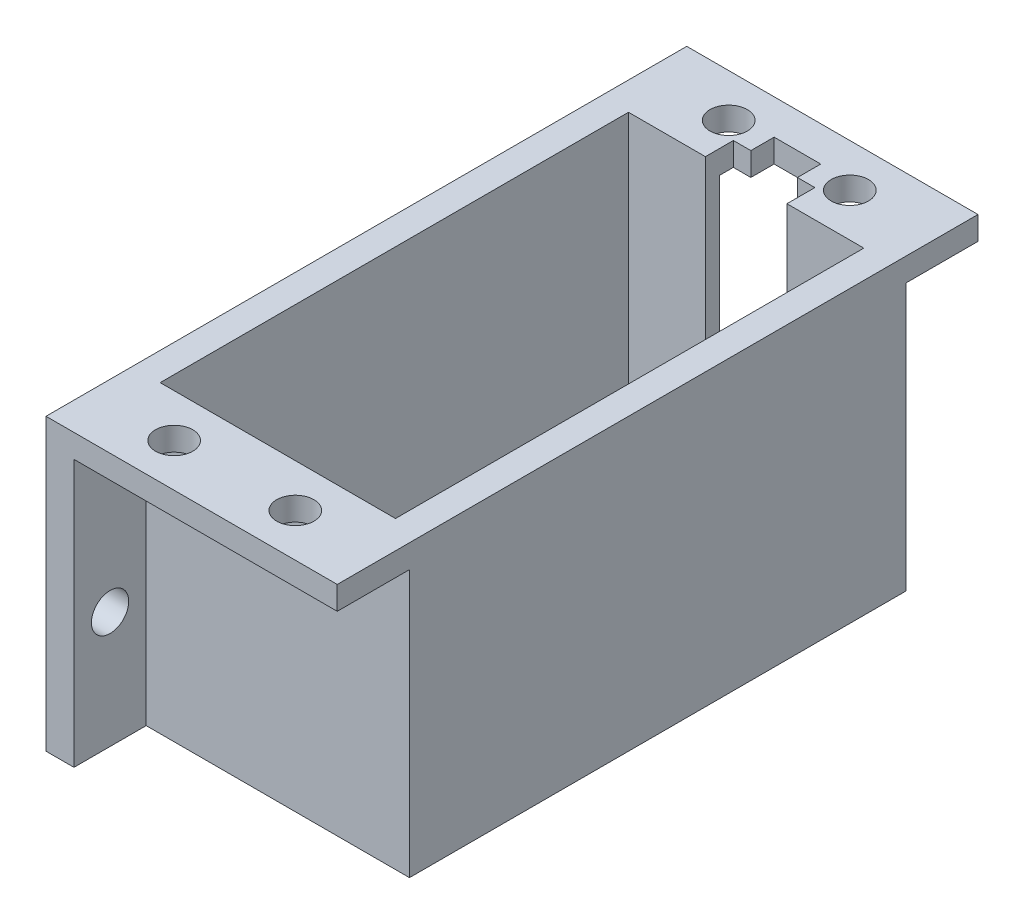
SolidWorks part; units mm, degrees
ref_plane "Front Plane" through (0, 0, 0) normal (0, 0, 1) x (1, 0, 0)
ref_plane "Top Plane" through (0, 0, 0) normal (0, 1, 0) x (1, 0, 0)
ref_plane "Right Plane" through (0, 0, 0) normal (1, 0, 0) x (0, 0, -1)
sketch "Sketch2" plane through (0, 0, 0) normal (0, 1, 0) x (1, 0, 0)
  line L1 (-37.5, 4) -> (37.5, 4)
  line L2 (-37.5, 4) -> (-37.5, -4)
  line L3 (-37.5, -4) -> (37.5, -4)
  line L4 (37.5, 4) -> (37.5, -4)
  line L5 (-37.5, 4) -> (37.5, -4) construction
  line L6 (-37.5, -4) -> (37.5, 4) construction
  circle A1 centre (-31.75, 0) radius 1.6
  circle A2 centre (31.75, 0) radius 1.6
  point P0 (0, 0)
extrude "Boss-Extrude1" add sketch "Sketch2" along normal blind 2
sketch "Sketch3" plane through (0, 2, 0) normal (0, 1, 0) x (1, 0, 0)
  line L1 (-12.5, -22.5) -> (12.5, -22.5)
  line L2 (-12.5, -22.5) -> (-12.5, -4)
  line L3 (-37.5, -4) -> (37.5, -4) construction
  line L4 (-12.5, -4) -> (12.5, -4)
  line L5 (12.5, -4) -> (12.5, -22.5)
  point P0 (0, -4)
  point P6 (0, -22.5)
extrude "Boss-Extrude2" add sketch "Sketch3" against normal up to surface (2 mm away) up to face at (0, 0, 0)
sketch "Sketch4" plane through (0, 0, -4) normal (0, 0, -1) x (-1, 0, 0)
  line L4 (-12.5, 0) -> (12.5, 0)
  line L5 (-12.5, 2) -> (-12.5, 0)
  line L6 (12.5, 2) -> (-12.5, 2)
  line L7 (12.5, 0) -> (12.5, 2)
  line L8 (-12.5, 0) -> (12.5, 0)
  line L9 (-12.5, 2) -> (-12.5, 0)
  line L10 (12.5, 2) -> (-12.5, 2)
  line L11 (12.5, 0) -> (12.5, 2)
  dimension "D1" = 0
extrude "Boss-Extrude3" add sketch "Sketch4" along normal blind 18.5
sketch "Sketch5" plane through (0, 2, 0) normal (0, 1, 0) x (1, 0, 0)
  line L1 (-5.1, 20.1) -> (5.1, 20.1)
  line L2 (-5.1, 20.1) -> (-5.1, -20.1)
  line L3 (-5.1, -20.1) -> (5.1, -20.1)
  line L4 (5.1, 20.1) -> (5.1, -20.1)
  line L5 (-5.1, 20.1) -> (5.1, -20.1) construction
  line L6 (-5.1, -20.1) -> (5.1, 20.1) construction
  point P0 (0, 0)
extrude "Cut-Extrude1" cut sketch "Sketch5" against normal blind 18.5
sketch "Sketch6" plane through (0, 2, 0) normal (0, 1, 0) x (1, 0, 0)
  line L0 (-12.5, 4) -> (-12.5, -4)
  line L1 (12.5, 4) -> (12.5, -4)
  line L3 (-5.1, 20.1) -> (5.1, 20.1)
  line L4 (-5.1, 20.1) -> (-5.1, -20.1)
  line L5 (-5.1, -20.1) -> (5.1, -20.1)
  line L6 (5.1, 20.1) -> (5.1, -20.1)
  line L12 (37.5, -4) -> (37.5, 4)
  line L13 (37.5, 4) -> (12.5, 4)
  line L14 (12.5, 4) -> (12.5, 22.5)
  line L15 (12.5, 22.5) -> (-12.5, 22.5)
  line L16 (-12.5, 22.5) -> (-12.5, 4)
  line L17 (-12.5, 4) -> (-37.5, 4)
  line L18 (-37.5, 4) -> (-37.5, -4)
  line L19 (-37.5, -4) -> (-12.5, -4)
  line L20 (-12.5, -4) -> (-12.5, -22.5)
  line L21 (-12.5, -22.5) -> (12.5, -22.5)
  line L22 (12.5, -22.5) -> (12.5, -4)
  line L23 (12.5, -4) -> (37.5, -4)
  line L26 (12.5, 4) -> (12.5, 22.5)
  line L27 (12.5, 22.5) -> (-12.5, 22.5)
  line L28 (-12.5, 22.5) -> (-12.5, 4)
  line L32 (-12.5, -4) -> (-12.5, -22.5)
  line L33 (-12.5, -22.5) -> (12.5, -22.5)
  line L34 (12.5, -22.5) -> (12.5, -4)
  dimension "D1" = 0
extrude "Boss-Extrude4" add sketch "Sketch6" along normal blind 24.9
sketch "Sketch8" plane through (0, 26.9, 0) normal (0, 1, 0) x (1, 0, 0)
  line L1 (-12.5, 22.5) -> (12.5, 22.5)
  line L2 (-12.5, 22.5) -> (-12.5, 29.5)
  line L3 (-12.5, 29.5) -> (12.5, 29.5)
  line L4 (12.5, 22.5) -> (12.5, 29.5)
  line L5 (-12.5, -22.5) -> (12.5, -22.5)
  line L6 (-12.5, -22.5) -> (-12.5, -29.5)
  line L7 (-12.5, -29.5) -> (12.5, -29.5)
  line L8 (12.5, -22.5) -> (12.5, -29.5)
extrude "Boss-Extrude5" add sketch "Sketch8" against normal blind 2
sketch "Sketch9" plane through (0, 24.9, 0) normal (0, -1, 0) x (1, 0, 0)
  circle A1 centre (5.2, 23.8) radius 1.6
  circle A2 centre (-5.2, 23.8) radius 1.6
  circle A3 centre (-5.2, -23.8) radius 1.6
  circle A4 centre (5.2, -23.8) radius 1.6
extrude "Cut-Extrude2" cut sketch "Sketch9" against normal blind 2
sketch "Sketch10" plane through (0, 0, 0) normal (0, -1, 0) x (1, 0, 0)
  line L1 (-10.1, 20.1) -> (10.1, 20.1)
  line L2 (-10.1, 20.1) -> (-10.1, -20.1)
  line L3 (-10.1, -20.1) -> (10.1, -20.1)
  line L4 (10.1, 20.1) -> (10.1, -20.1)
  line L5 (-10.1, 20.1) -> (10.1, -20.1) construction
  line L6 (-10.1, -20.1) -> (10.1, 20.1) construction
  point P0 (0, 0)
extrude "Cut-Extrude3" cut sketch "Sketch10" against normal blind 77
sketch "Sketch11" plane through (0, 0, 0) normal (0, -1, 0) x (1, 0, 0)
  line L1 (3.5, -20.1) -> (3.5, -22.5)
  line L2 (12.5, -22.5) -> (-12.5, -22.5) construction
  line L3 (3.5, -22.5) -> (-3.5, -22.5)
  line L4 (-3.5, -22.5) -> (-3.5, -20.1)
  line L5 (-3.5, -20.1) -> (3.5, -20.1)
extrude "Cut-Extrude4" cut sketch "Sketch11" against normal blind 77
sketch "Sketch12" plane through (0, 0, 0) normal (0, -1, 0) x (1, 0, 0)
  line L0 (-12.5, 22.5) -> (-12.5, 29.5)
  line L1 (-12.5, 29.5) -> (-10.1, 29.5)
  line L2 (-12.5, 29.5) -> (12.5, 29.5) construction
  line L3 (-10.1, 29.5) -> (-10.1, 22.5)
  line L4 (12.5, 22.5) -> (6.1327, 22.5) construction
  line L5 (-10.1, 22.5) -> (-12.5, 22.5)
  line L6 (-12.5, -22.5) -> (-6.1327, -22.5) construction
  line L7 (-10.1, -22.5) -> (-12.5, -22.5)
  line L8 (-10.1, -22.5) -> (-10.1, -29.5)
  line L9 (-10.1, -29.5) -> (-12.5, -29.5)
  line L10 (-12.5, -22.5) -> (-12.5, -29.5)
  line L11 (12.5, 22.5) -> (-12.5, 22.5) construction
  line L12 (12.5, 29.5) -> (10.1, 29.5)
  line L13 (12.5, 29.5) -> (12.5, 22.5)
  line L14 (12.5, 22.5) -> (10.1, 22.5)
  line L15 (10.1, 29.5) -> (10.1, 22.5)
  line L16 (3.5, -22.5) -> (4.2673, -22.5) construction
  line L17 (10.1, -22.5) -> (12.5, -22.5)
  line L18 (10.1, -22.5) -> (10.1, -29.5)
  line L19 (10.1, -29.5) -> (12.5, -29.5)
  line L20 (12.5, -22.5) -> (12.5, -29.5)
extrude "Boss-Extrude6" add sketch "Sketch12" against normal up to surface (24.9 mm away) up to face at (0, 24.9, 24.975)
sketch "Sketch13" plane through (0, 26.9, 0) normal (0, 1, 0) x (1, 0, 0)
  line L0 (3.5, 22.5) -> (-3.5, 22.5) construction
  line L1 (-2, 24.5) -> (2, 24.5)
  line L2 (-2, 24.5) -> (-2, 20.5)
  line L3 (-2, 20.5) -> (2, 20.5)
  line L4 (2, 24.5) -> (2, 20.5)
  line L5 (-2, 24.5) -> (2, 20.5) construction
  line L6 (-2, 20.5) -> (2, 24.5) construction
  point P0 (0, 22.5)
extrude "Cut-Extrude5" cut sketch "Sketch13" against normal blind 77
sketch "Sketch14" plane through (0, 2, 0) normal (0, 1, 0) x (1, 0, 0)
  line L4 (-12.5, -4) -> (-12.5, 4)
  line L5 (-12.5, 4) -> (-37.5, 4)
  line L6 (-37.5, 4) -> (-37.5, -4)
  line L7 (-37.5, -4) -> (-12.5, -4)
  line L8 (-12.5, -4) -> (-12.5, 4)
  line L9 (-12.5, 4) -> (-37.5, 4)
  line L10 (-37.5, 4) -> (-37.5, -4)
  line L11 (-37.5, -4) -> (-12.5, -4)
  line L12 (12.5, 4) -> (12.5, -4)
  line L13 (12.5, -4) -> (37.5, -4)
  line L14 (37.5, -4) -> (37.5, 4)
  line L15 (37.5, 4) -> (12.5, 4)
  line L16 (12.5, 4) -> (12.5, -4)
  line L17 (12.5, -4) -> (37.5, -4)
  line L18 (37.5, -4) -> (37.5, 4)
  line L19 (37.5, 4) -> (12.5, 4)
  circle A0 centre (-31.75, 0) radius 1.6 construction
  circle A1 centre (-31.75, 0) radius 1.6
  circle A2 centre (31.75, 0) radius 1.6 construction
  circle A3 centre (31.75, 0) radius 1.6
  dimension "D1" = 0
  dimension "D2" = 0
extrude "Boss-Extrude7" add sketch "Sketch14" along normal blind 2
sketch "Sketch15" plane through (0, 0, 0) normal (0, -1, 0) x (1, 0, 0)
  line L28 (10.1, -20.1) -> (3.5, -20.1)
  line L29 (3.5, -20.1) -> (3.5, -22.5)
  line L30 (3.5, -22.5) -> (10.1, -22.5)
  line L31 (10.1, -22.5) -> (10.1, -29.5)
  line L32 (10.1, -29.5) -> (12.5, -29.5)
  line L33 (12.5, -29.5) -> (12.5, -4)
  line L34 (12.5, -4) -> (37.5, -4)
  line L35 (37.5, -4) -> (37.5, 4)
  line L36 (37.5, 4) -> (12.5, 4)
  line L37 (12.5, 4) -> (12.5, 29.5)
  line L38 (12.5, 29.5) -> (10.1, 29.5)
  line L39 (10.1, 29.5) -> (10.1, 22.5)
  line L40 (10.1, 22.5) -> (-10.1, 22.5)
  line L41 (-10.1, 22.5) -> (-10.1, 29.5)
  line L42 (-10.1, 29.5) -> (-12.5, 29.5)
  line L43 (-12.5, 29.5) -> (-12.5, 4)
  line L44 (-12.5, 4) -> (-37.5, 4)
  line L45 (-37.5, 4) -> (-37.5, -4)
  line L46 (-37.5, -4) -> (-12.5, -4)
  line L47 (-12.5, -4) -> (-12.5, -29.5)
  line L48 (-12.5, -29.5) -> (-10.1, -29.5)
  line L49 (-10.1, -29.5) -> (-10.1, -22.5)
  line L50 (-10.1, -22.5) -> (-3.5, -22.5)
  line L51 (-3.5, -22.5) -> (-3.5, -20.1)
  line L52 (-3.5, -20.1) -> (-10.1, -20.1)
  line L53 (-10.1, -20.1) -> (-10.1, 20.1)
  line L54 (-10.1, 20.1) -> (10.1, 20.1)
  line L55 (10.1, 20.1) -> (10.1, -20.1)
  line L56 (10.1, -20.1) -> (3.5, -20.1)
  line L57 (3.5, -20.1) -> (3.5, -22.5)
  line L58 (3.5, -22.5) -> (10.1, -22.5)
  line L59 (10.1, -22.5) -> (10.1, -29.5)
  line L60 (10.1, -29.5) -> (12.5, -29.5)
  line L61 (12.5, -29.5) -> (12.5, -4)
  line L62 (12.5, -4) -> (37.5, -4)
  line L63 (37.5, -4) -> (37.5, 4)
  line L64 (37.5, 4) -> (12.5, 4)
  line L65 (12.5, 4) -> (12.5, 29.5)
  line L66 (12.5, 29.5) -> (10.1, 29.5)
  line L67 (10.1, 29.5) -> (10.1, 22.5)
  line L68 (10.1, 22.5) -> (-10.1, 22.5)
  line L69 (-10.1, 22.5) -> (-10.1, 29.5)
  line L70 (-10.1, 29.5) -> (-12.5, 29.5)
  line L71 (-12.5, 29.5) -> (-12.5, 4)
  line L72 (-12.5, 4) -> (-37.5, 4)
  line L73 (-37.5, 4) -> (-37.5, -4)
  line L74 (-37.5, -4) -> (-12.5, -4)
  line L75 (-12.5, -4) -> (-12.5, -29.5)
  line L76 (-12.5, -29.5) -> (-10.1, -29.5)
  line L77 (-10.1, -29.5) -> (-10.1, -22.5)
  line L78 (-10.1, -22.5) -> (-3.5, -22.5)
  line L79 (-3.5, -22.5) -> (-3.5, -20.1)
  line L80 (-3.5, -20.1) -> (-10.1, -20.1)
  line L81 (-10.1, -20.1) -> (-10.1, 20.1)
  line L82 (-10.1, 20.1) -> (10.1, 20.1)
  line L83 (10.1, 20.1) -> (10.1, -20.1)
  dimension "D1" = 0
extrude "Cut-Extrude6" cut sketch "Sketch15" against normal blind 2
chamfer "Chamfer1" distance 10 angle 45 2 edges at (12.5, 4, 0) (-12.5, 4, 0)
sketch "Sketch16" plane through (0, 0, 22.5) normal (0, 0, 1) x (1, 0, 0)
  line L8 (-10.1, 2) -> (10.1, 2)
  line L9 (10.1, 2) -> (10.1, 24.9)
  line L10 (10.1, 24.9) -> (6.1327, 24.9)
  line L11 (6.1327, 24.9) -> (4.2673, 24.9)
  line L12 (4.2673, 24.9) -> (-4.2673, 24.9)
  line L13 (-4.2673, 24.9) -> (-6.1327, 24.9)
  line L14 (-6.1327, 24.9) -> (-10.1, 24.9)
  line L15 (-10.1, 24.9) -> (-10.1, 2)
  line L16 (-10.1, 2) -> (10.1, 2)
  line L17 (10.1, 2) -> (10.1, 24.9)
  line L18 (10.1, 24.9) -> (6.1327, 24.9)
  line L19 (6.1327, 24.9) -> (4.2673, 24.9)
  line L20 (4.2673, 24.9) -> (-4.2673, 24.9)
  line L21 (-4.2673, 24.9) -> (-6.1327, 24.9)
  line L22 (-6.1327, 24.9) -> (-10.1, 24.9)
  line L23 (-10.1, 24.9) -> (-10.1, 2)
  dimension "D1" = 0
extrude "Cut-Extrude7" cut sketch "Sketch16" against normal blind 1.2
sketch "Sketch17" plane through (0, 0, -22.5) normal (0, 0, -1) x (-1, 0, 0)
  line L12 (10.1, 2) -> (10.1, 24.9)
  line L13 (-10.1, 2) -> (10.1, 2)
  line L14 (-10.1, 24.9) -> (-10.1, 2)
  line L15 (10.1, 24.9) -> (-10.1, 24.9)
  line L16 (10.1, 2) -> (10.1, 24.9)
  line L17 (-10.1, 2) -> (10.1, 2)
  line L18 (-10.1, 24.9) -> (-10.1, 2)
  line L19 (10.1, 24.9) -> (-10.1, 24.9)
  dimension "D1" = 0
extrude "Cut-Extrude8" cut sketch "Sketch17" against normal blind 1.2
sketch "Sketch18" plane through (0, 0, -29.5) normal (0, 0, -1) x (-1, 0, 0)
  line L8 (10.1, 2) -> (12.5, 2)
  line L9 (12.5, 2) -> (12.5, 26.9)
  line L10 (12.5, 26.9) -> (-12.5, 26.9)
  line L11 (-12.5, 26.9) -> (-12.5, 2)
  line L12 (-12.5, 2) -> (-10.1, 2)
  line L13 (-10.1, 2) -> (-10.1, 24.9)
  line L14 (-10.1, 24.9) -> (10.1, 24.9)
  line L15 (10.1, 24.9) -> (10.1, 2)
  line L16 (10.1, 2) -> (12.5, 2)
  line L17 (12.5, 2) -> (12.5, 26.9)
  line L18 (12.5, 26.9) -> (-12.5, 26.9)
  line L19 (-12.5, 26.9) -> (-12.5, 2)
  line L20 (-12.5, 2) -> (-10.1, 2)
  line L21 (-10.1, 2) -> (-10.1, 24.9)
  line L22 (-10.1, 24.9) -> (10.1, 24.9)
  line L23 (10.1, 24.9) -> (10.1, 2)
  dimension "D1" = 0
extrude "Cut-Extrude9" cut sketch "Sketch18" against normal blind 2
sketch "Sketch19" plane through (0, 0, 29.5) normal (0, 0, 1) x (1, 0, 0)
  line L8 (10.1, 2) -> (12.5, 2)
  line L9 (12.5, 2) -> (12.5, 26.9)
  line L10 (12.5, 26.9) -> (-12.5, 26.9)
  line L11 (-12.5, 26.9) -> (-12.5, 2)
  line L12 (-12.5, 2) -> (-10.1, 2)
  line L13 (-10.1, 2) -> (-10.1, 24.9)
  line L14 (-10.1, 24.9) -> (10.1, 24.9)
  line L15 (10.1, 24.9) -> (10.1, 2)
  line L16 (10.1, 2) -> (12.5, 2)
  line L17 (12.5, 2) -> (12.5, 26.9)
  line L18 (12.5, 26.9) -> (-12.5, 26.9)
  line L19 (-12.5, 26.9) -> (-12.5, 2)
  line L20 (-12.5, 2) -> (-10.1, 2)
  line L21 (-10.1, 2) -> (-10.1, 24.9)
  line L22 (-10.1, 24.9) -> (10.1, 24.9)
  line L23 (10.1, 24.9) -> (10.1, 2)
  dimension "D1" = 0
extrude "Cut-Extrude10" cut sketch "Sketch19" against normal blind 2
sketch "Sketch20" plane through (0, 2, 0) normal (0, -1, 0) x (1, 0, 0)
  line L0 (-12.5, 4) -> (-12.5, -4)
  line L1 (12.5, 4) -> (12.5, -4)
  line L28 (-10.1, 27.5) -> (-12.5, 27.5)
  line L29 (-12.5, 27.5) -> (-12.5, 4)
  line L30 (-12.5, 4) -> (-37.5, 4)
  line L31 (-37.5, 4) -> (-37.5, -4)
  line L32 (-37.5, -4) -> (-12.5, -4)
  line L33 (-12.5, -4) -> (-12.5, -27.5)
  line L34 (-12.5, -27.5) -> (-10.1, -27.5)
  line L35 (-10.1, -27.5) -> (-10.1, -21.3)
  line L36 (-10.1, -21.3) -> (-3.5, -21.3)
  line L37 (-3.5, -21.3) -> (-3.5, -20.1)
  line L38 (-3.5, -20.1) -> (-10.1, -20.1)
  line L39 (-10.1, -20.1) -> (-10.1, 20.1)
  line L40 (-10.1, 20.1) -> (10.1, 20.1)
  line L41 (10.1, 20.1) -> (10.1, -20.1)
  line L42 (10.1, -20.1) -> (3.5, -20.1)
  line L43 (3.5, -20.1) -> (3.5, -21.3)
  line L44 (3.5, -21.3) -> (10.1, -21.3)
  line L45 (10.1, -21.3) -> (10.1, -27.5)
  line L46 (10.1, -27.5) -> (12.5, -27.5)
  line L47 (12.5, -27.5) -> (12.5, -4)
  line L48 (12.5, -4) -> (37.5, -4)
  line L49 (37.5, -4) -> (37.5, 4)
  line L50 (37.5, 4) -> (12.5, 4)
  line L51 (12.5, 4) -> (12.5, 27.5)
  line L52 (12.5, 27.5) -> (10.1, 27.5)
  line L53 (10.1, 27.5) -> (10.1, 21.3)
  line L54 (10.1, 21.3) -> (-10.1, 21.3)
  line L55 (-10.1, 21.3) -> (-10.1, 27.5)
  line L58 (-12.5, 4) -> (-37.5, 4)
  line L59 (-37.5, 4) -> (-37.5, -4)
  line L60 (-37.5, -4) -> (-12.5, -4)
  line L76 (12.5, -4) -> (37.5, -4)
  line L77 (37.5, -4) -> (37.5, 4)
  line L78 (37.5, 4) -> (12.5, 4)
  dimension "D1" = 0
extrude "Cut-Extrude11" cut sketch "Sketch20" against normal blind 156
sketch "Sketch21" plane through (-10.1, 0, 0) normal (1, 0, 0) x (0, 0, -1)
  line L4 (-21.3, 24.9) -> (-27.5, 24.9)
  line L5 (-27.5, 24.9) -> (-27.5, 2)
  line L6 (-27.5, 2) -> (-21.3, 2)
  line L7 (-21.3, 2) -> (-21.3, 24.9)
  line L8 (-21.3, 24.9) -> (-27.5, 24.9)
  line L9 (-27.5, 24.9) -> (-27.5, 2)
  line L10 (-27.5, 2) -> (-21.3, 2)
  line L11 (-21.3, 2) -> (-21.3, 24.9)
  line L12 (21.3, 2) -> (27.5, 2)
  line L13 (27.5, 2) -> (27.5, 24.9)
  line L14 (27.5, 24.9) -> (21.3, 24.9)
  line L15 (21.3, 24.9) -> (21.3, 2)
  line L16 (21.3, 2) -> (27.5, 2)
  line L17 (27.5, 2) -> (27.5, 24.9)
  line L18 (27.5, 24.9) -> (21.3, 24.9)
  line L19 (21.3, 24.9) -> (21.3, 2)
  dimension "D1" = 0
  dimension "D2" = 0
extrude "Cut-Extrude12" cut sketch "Sketch21" along normal blind 55
sketch "Sketch22" plane through (-10.1, 0, 0) normal (1, 0, 0) x (0, 0, -1)
  circle A0 centre (-24.4, 12) radius 1.6
  circle A1 centre (24.4, 12) radius 1.6
extrude "Cut-Extrude13" cut sketch "Sketch22" against normal blind 55
